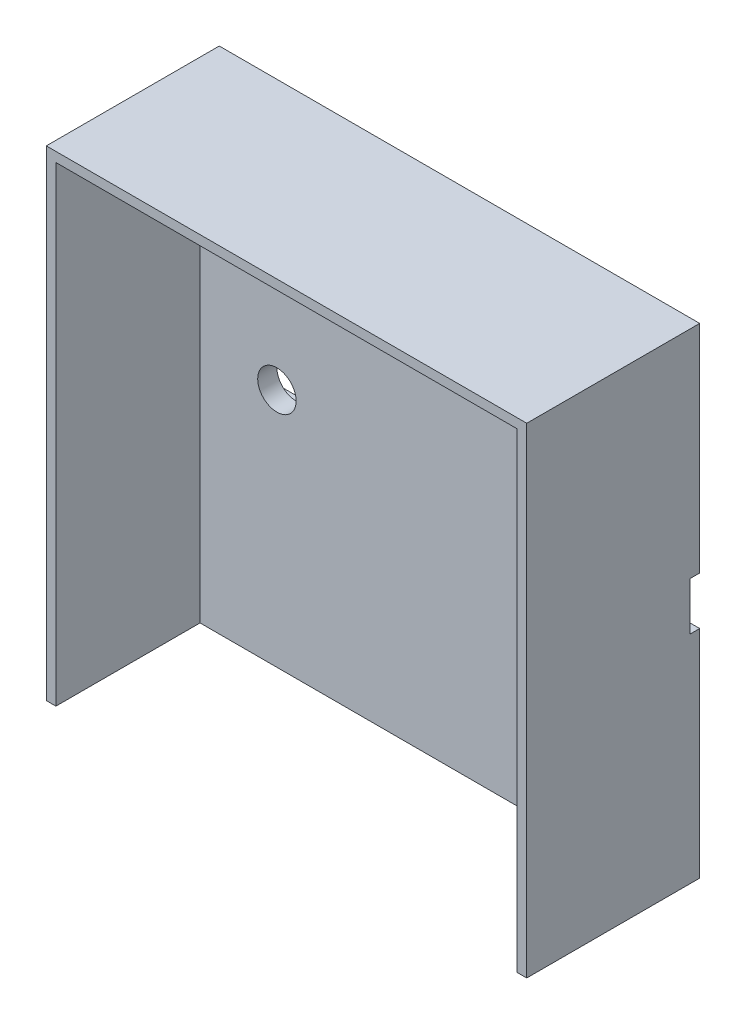
SolidWorks part; units mm, degrees
ref_plane "Přední rovina" through (0, 0, 0) normal (0, 0, 1) x (1, 0, 0)
ref_plane "Horní rovina" through (0, 0, 0) normal (0, 1, 0) x (1, 0, 0)
ref_plane "Pravá rovina" through (0, 0, 0) normal (1, 0, 0) x (0, 0, -1)
sketch "Skica1" plane through (0, 0, 0) normal (0, 0, 1) x (1, 0, 0)
  line L1 (25, 25) -> (-25, 25)
  line L2 (25, 25) -> (25, -25)
  line L3 (25, -25) -> (-25, -25)
  line L4 (-25, 25) -> (-25, -25)
  line L5 (25, 25) -> (-25, -25) construction
  line L6 (25, -25) -> (-25, 25) construction
  point P0 (0, 0)
  point P5 (-27.5, 0)
  point P11 (4.5, 0)
  dimension "D1" = 50
  dimension "D2" = 50
extrude "Přidat vysunutím2" add sketch "Skica1" along normal blind 3 contours L2 L1 L4 L3
sketch "Skica5" plane through (0, 0, 0) normal (0, 0, -1) x (-1, 0, 0)
  line L10 (25, 25) -> (25, -25) construction
  line L11 (-25, 2.5) -> (25, 2.5)
  line L12 (-25, 2.5) -> (-25, -2.5)
  line L13 (-25, -2.5) -> (25, -2.5)
  line L14 (25, 2.5) -> (25, -2.5)
  line L15 (-25, 2.5) -> (25, -2.5) construction
  line L16 (-25, -2.5) -> (25, 2.5) construction
  point P0 (0, 0)
  dimension "D1" = 5
extrude "Odebrat vysunutím3" cut sketch "Skica5" against normal blind 1 contours L11 L14 L13 L12
sketch "Skica14" plane through (0, 0, 3) normal (0, 0, 1) x (1, 0, 0)
  line L1 (-25, 25) -> (25, 25)
  line L2 (-25, 25) -> (-25, -25)
  line L3 (-25, -25) -> (25, -25)
  line L4 (25, 25) -> (25, -25)
  line L5 (-24, 24) -> (24, 24)
  line L6 (-24, 24) -> (-24, -25)
  line L7 (-24, -25) -> (24, -25)
  line L8 (24, 24) -> (24, -25)
  line M13 (-25, -25) -> (25, -25)
  line M14 (25, -25) -> (25, 25)
  line M15 (25, 25) -> (-25, 25)
  line M16 (-25, 25) -> (-25, -25)
  dimension "D1" = 1
  dimension "D2" = 1
  dimension "D3" = 1
  dimension "D4" = 0
extrude "Přidat vysunutím9" add sketch "Skica14" along normal blind 15 contours L5 L8 L6 M13 M14 M15 M16
sketch "Skica17" plane through (0, 0, 1) normal (0, 0, -1) x (-1, 0, 0)
  line L0 (-25, 2.5) -> (-25, -2.5) construction
  line L1 (-10, -2.5) -> (-10, 2.5) construction
  line L2 (25, 2.5) -> (25, -2.5) construction
  circle A0 centre (-16, 0) radius 2
  circle A1 centre (16, 0) radius 2
  dimension "D1" = 4
  dimension "D2" = 4
  dimension "D3" = 9
  dimension "D4" = 6
  dimension "D5" = 9
extrude "Odebrat vysunutím8" cut sketch "Skica17" against normal blind 4
